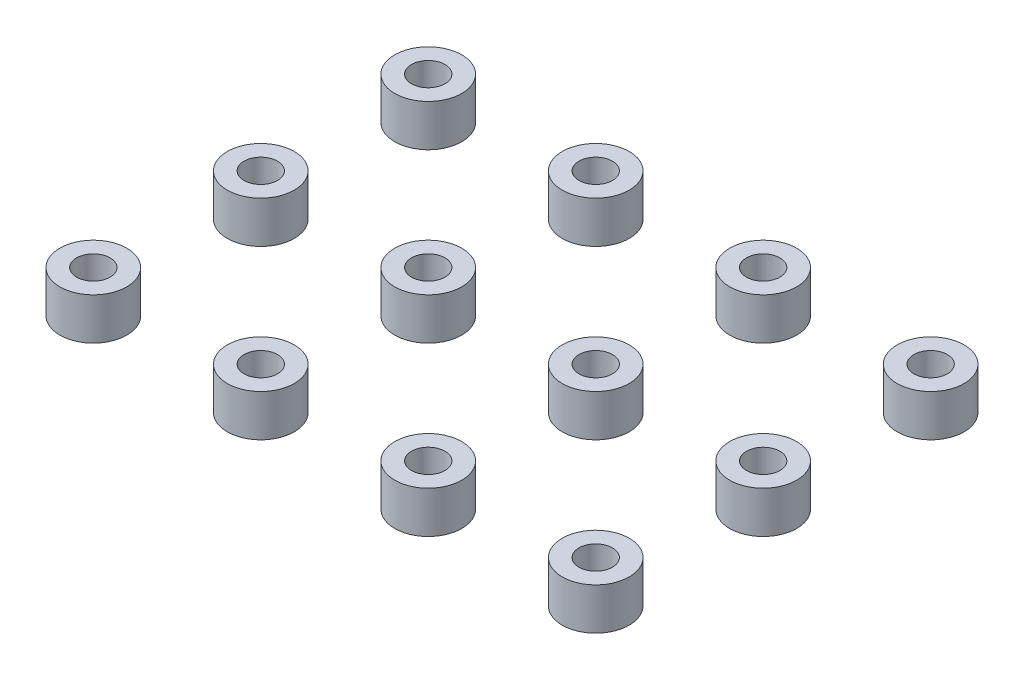
SolidWorks part; units mm, degrees
ref_plane "Front Plane" through (0, 0, 0) normal (0, 0, 1) x (1, 0, 0)
ref_plane "Top Plane" through (0, 0, 0) normal (0, 1, 0) x (1, 0, 0)
ref_plane "Right Plane" through (0, 0, 0) normal (1, 0, 0) x (0, 0, -1)
sketch "Sketch1" plane through (0, 0, 0) normal (0, 1, 0) x (1, 0, 0)
  circle A0 centre (-30, 30) radius 2
  circle A1 centre (-30, 30) radius 4
  circle A2 centre (-10, 30) radius 2
  circle A3 centre (-10, 30) radius 4
  circle A4 centre (10, 30) radius 2
  circle A5 centre (10, 30) radius 4
  circle A6 centre (30, 30) radius 2
  circle A7 centre (30, 30) radius 4
  circle A8 centre (-10, 50) radius 2
  circle A9 centre (-10, 50) radius 4
  circle A10 centre (10, 50) radius 2
  circle A11 centre (10, 50) radius 4
  circle A12 centre (30, 50) radius 2
  circle A13 centre (30, 50) radius 4
  circle A14 centre (-10, 70) radius 2
  circle A15 centre (-10, 70) radius 4
  circle A16 centre (10, 70) radius 2
  circle A17 centre (10, 70) radius 4
  circle A18 centre (30, 70) radius 2
  circle A19 centre (30, 70) radius 4
  circle A20 centre (-30, 50) radius 2
  circle A21 centre (-30, 50) radius 4
  circle A22 centre (-30, 70) radius 2
  circle A23 centre (-30, 70) radius 4
  dimension "D3" = 4
  dimension "D4" = 8
  dimension "D1" = 30
  dimension "D2" = 30
  dimension "D5" = 4
  dimension "D6" = 3
extrude "Boss-Extrude1" add sketch "Sketch1" along normal blind 5
